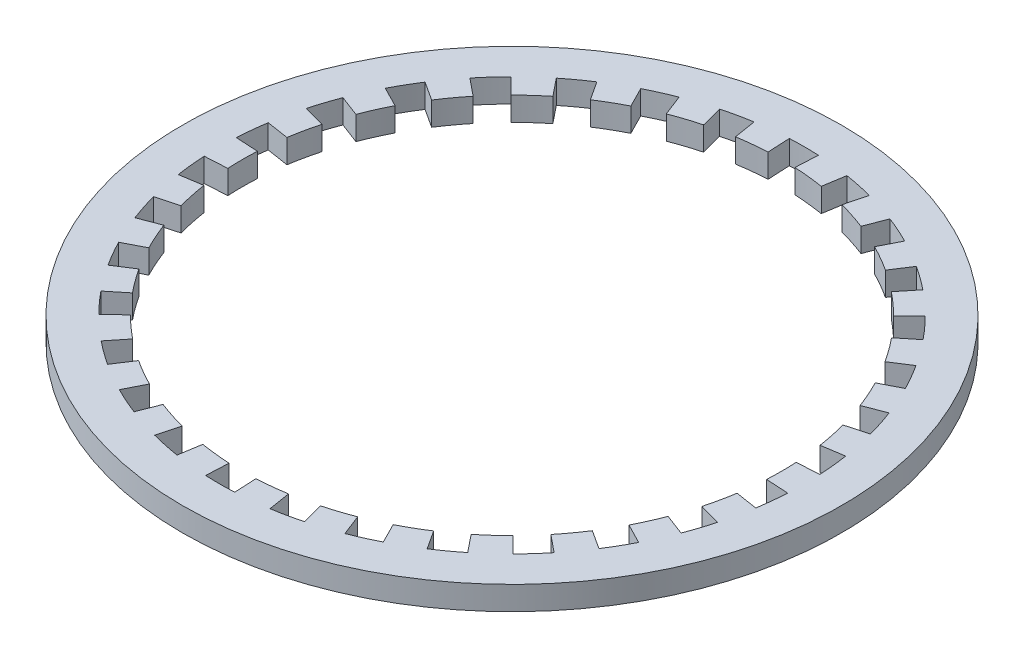
SolidWorks part; units mm, degrees
ref_plane "Front Plane" through (0, 0, 0) normal (0, 0, 1) x (1, 0, 0)
ref_plane "Top Plane" through (0, 0, 0) normal (0, 1, 0) x (1, 0, 0)
ref_plane "Right Plane" through (0, 0, 0) normal (1, 0, 0) x (0, 0, -1)
sketch "Sketch1" plane through (0, 0, 0) normal (0, 1, 0) x (1, 0, 0)
  circle A0 centre (0, 0) radius 7.94
  circle A1 centre (0, 0) radius 6.5
  dimension "D1" = 15.88
  dimension "D2" = 13
extrude "Boss-Extrude1" add sketch "Sketch1" along normal blind 0.57
sketch "Sketch2" plane through (0, 0.57, 0) normal (0, 1, 0) x (1, 0, 0)
  line L0 (0, 7.94) -> (0, -7.94) construction
  line L1 (0.35, 7.0313) -> (0, 0) construction
  line L2 (0, 0) -> (-0.35, 7.0313) construction
  line L3 (-0.35, 7.0313) -> (0.35, 7.0313) construction
  line L4 (0, 7.0313) -> (0, 0) construction
  line L5 (-0.35, 7.0313) -> (-0.3232, 6.492)
  line L6 (0.35, 7.0313) -> (0.3232, 6.492)
  line L7 (1.8042, 6.8049) -> (1.6658, 6.2829)
  line L8 (1.1195, 6.9504) -> (1.0337, 6.4173)
  line L9 (3.1796, 6.281) -> (2.9357, 5.7993)
  line L10 (2.5401, 6.5658) -> (2.3453, 6.0621)
  line L11 (4.416, 5.4827) -> (4.0773, 5.0622)
  line L12 (3.8497, 5.8942) -> (3.5544, 5.4421)
  line L13 (5.4595, 4.4448) -> (5.0407, 4.1038)
  line L14 (4.9911, 4.965) -> (4.6082, 4.5841)
  line L15 (6.2643, 3.2125) -> (5.7838, 2.9661)
  line L16 (5.9143, 3.8188) -> (5.4606, 3.5258)
  line L17 (6.7953, 1.8399) -> (6.2741, 1.6988)
  line L18 (6.579, 2.5057) -> (6.0744, 2.3135)
  line L19 (7.0294, 0.3869) -> (6.4902, 0.3572)
  line L20 (6.9562, 1.0831) -> (6.4226, 1)
  line L21 (6.9562, -1.0831) -> (6.4226, -1)
  line L22 (7.0294, -0.3869) -> (6.4902, -0.3572)
  line L23 (6.579, -2.5057) -> (6.0744, -2.3135)
  line L24 (6.7953, -1.8399) -> (6.2741, -1.6988)
  line L25 (5.9143, -3.8188) -> (5.4606, -3.5258)
  line L26 (6.2643, -3.2125) -> (5.7838, -2.9661)
  line L27 (4.9911, -4.965) -> (4.6082, -4.5841)
  line L28 (5.4595, -4.4448) -> (5.0407, -4.1038)
  line L29 (3.8497, -5.8942) -> (3.5544, -5.4421)
  line L30 (4.416, -5.4827) -> (4.0773, -5.0622)
  line L31 (2.5401, -6.5658) -> (2.3453, -6.0621)
  line L32 (3.1796, -6.281) -> (2.9357, -5.7993)
  line L33 (1.1195, -6.9504) -> (1.0337, -6.4173)
  line L34 (1.8042, -6.8049) -> (1.6658, -6.2829)
  line L35 (-0.35, -7.0313) -> (-0.3232, -6.492)
  line L36 (0.35, -7.0313) -> (0.3232, -6.492)
  line L37 (-1.8042, -6.8049) -> (-1.6658, -6.2829)
  line L38 (-1.1195, -6.9504) -> (-1.0337, -6.4173)
  line L39 (-3.1796, -6.281) -> (-2.9357, -5.7993)
  line L40 (-2.5401, -6.5658) -> (-2.3453, -6.0621)
  line L41 (-4.416, -5.4827) -> (-4.0773, -5.0622)
  line L42 (-3.8497, -5.8942) -> (-3.5544, -5.4421)
  line L43 (-5.4595, -4.4448) -> (-5.0407, -4.1038)
  line L44 (-4.9911, -4.965) -> (-4.6082, -4.5841)
  line L45 (-6.2643, -3.2125) -> (-5.7838, -2.9661)
  line L46 (-5.9143, -3.8188) -> (-5.4606, -3.5258)
  line L47 (-6.7953, -1.8399) -> (-6.2741, -1.6988)
  line L48 (-6.579, -2.5057) -> (-6.0744, -2.3135)
  line L49 (-7.0294, -0.3869) -> (-6.4902, -0.3572)
  line L50 (-6.9562, -1.0831) -> (-6.4226, -1)
  line L51 (-6.9562, 1.0831) -> (-6.4226, 1)
  line L52 (-7.0294, 0.3869) -> (-6.4902, 0.3572)
  line L53 (-6.579, 2.5057) -> (-6.0744, 2.3135)
  line L54 (-6.7953, 1.8399) -> (-6.2741, 1.6988)
  line L55 (-5.9143, 3.8188) -> (-5.4606, 3.5258)
  line L56 (-6.2643, 3.2125) -> (-5.7838, 2.9661)
  line L57 (-4.9911, 4.965) -> (-4.6082, 4.5841)
  line L58 (-5.4595, 4.4448) -> (-5.0407, 4.1038)
  line L59 (-3.8497, 5.8942) -> (-3.5544, 5.4421)
  line L60 (-4.416, 5.4827) -> (-4.0773, 5.0622)
  line L61 (-2.5401, 6.5658) -> (-2.3453, 6.0621)
  line L62 (-3.1796, 6.281) -> (-2.9357, 5.7993)
  line L63 (-1.1195, 6.9504) -> (-1.0337, 6.4173)
  line L64 (-1.8042, 6.8049) -> (-1.6658, 6.2829)
  circle A0 centre (0, 0) radius 7.94 construction
  circle A1 centre (0, 0) radius 6.5 construction
  arc A2 (0.3232, 6.492) -> (-0.3232, 6.492) centre (0, 0) ccw
  arc A3 (1.8042, 6.8049) -> (1.1195, 6.9504) centre (0, 0) ccw
  arc A4 (1.6658, 6.2829) -> (1.0337, 6.4173) centre (0, 0) ccw
  circle A5 centre (0, 0) radius 7.04
  arc A6 (0.35, 7.0313) -> (-0.35, 7.0313) centre (0, 0) ccw
  arc A7 (3.1796, 6.281) -> (2.5401, 6.5658) centre (0, 0) ccw
  arc A8 (2.9357, 5.7993) -> (2.3453, 6.0621) centre (0, 0) ccw
  arc A9 (4.416, 5.4827) -> (3.8497, 5.8942) centre (0, 0) ccw
  arc A10 (4.0773, 5.0622) -> (3.5544, 5.4421) centre (0, 0) ccw
  arc A11 (5.4595, 4.4448) -> (4.9911, 4.965) centre (0, 0) ccw
  arc A12 (5.0407, 4.1038) -> (4.6082, 4.5841) centre (0, 0) ccw
  arc A13 (6.2643, 3.2125) -> (5.9143, 3.8188) centre (0, 0) ccw
  arc A14 (5.7838, 2.9661) -> (5.4606, 3.5258) centre (0, 0) ccw
  arc A15 (6.7953, 1.8399) -> (6.579, 2.5057) centre (0, 0) ccw
  arc A16 (6.2741, 1.6988) -> (6.0744, 2.3135) centre (0, 0) ccw
  arc A17 (7.0294, 0.3869) -> (6.9562, 1.0831) centre (0, 0) ccw
  arc A18 (6.4902, 0.3572) -> (6.4226, 1) centre (0, 0) ccw
  arc A19 (6.9562, -1.0831) -> (7.0294, -0.3869) centre (0, 0) ccw
  arc A20 (6.4226, -1) -> (6.4902, -0.3572) centre (0, 0) ccw
  arc A21 (6.579, -2.5057) -> (6.7953, -1.8399) centre (0, 0) ccw
  arc A22 (6.0744, -2.3135) -> (6.2741, -1.6988) centre (0, 0) ccw
  arc A23 (5.9143, -3.8188) -> (6.2643, -3.2125) centre (0, 0) ccw
  arc A24 (5.4606, -3.5258) -> (5.7838, -2.9661) centre (0, 0) ccw
  arc A25 (4.9911, -4.965) -> (5.4595, -4.4448) centre (0, 0) ccw
  arc A26 (4.6082, -4.5841) -> (5.0407, -4.1038) centre (0, 0) ccw
  arc A27 (3.8497, -5.8942) -> (4.416, -5.4827) centre (0, 0) ccw
  arc A28 (3.5544, -5.4421) -> (4.0773, -5.0622) centre (0, 0) ccw
  arc A29 (2.5401, -6.5658) -> (3.1796, -6.281) centre (0, 0) ccw
  arc A30 (2.3453, -6.0621) -> (2.9357, -5.7993) centre (0, 0) ccw
  arc A31 (1.1195, -6.9504) -> (1.8042, -6.8049) centre (0, 0) ccw
  arc A32 (1.0337, -6.4173) -> (1.6658, -6.2829) centre (0, 0) ccw
  arc A33 (-0.35, -7.0313) -> (0.35, -7.0313) centre (0, 0) ccw
  arc A34 (-0.3232, -6.492) -> (0.3232, -6.492) centre (0, 0) ccw
  arc A35 (-1.8042, -6.8049) -> (-1.1195, -6.9504) centre (0, 0) ccw
  arc A36 (-1.6658, -6.2829) -> (-1.0337, -6.4173) centre (0, 0) ccw
  arc A37 (-3.1796, -6.281) -> (-2.5401, -6.5658) centre (0, 0) ccw
  arc A38 (-2.9357, -5.7993) -> (-2.3453, -6.0621) centre (0, 0) ccw
  arc A39 (-4.416, -5.4827) -> (-3.8497, -5.8942) centre (0, 0) ccw
  arc A40 (-4.0773, -5.0622) -> (-3.5544, -5.4421) centre (0, 0) ccw
  arc A41 (-5.4595, -4.4448) -> (-4.9911, -4.965) centre (0, 0) ccw
  arc A42 (-5.0407, -4.1038) -> (-4.6082, -4.5841) centre (0, 0) ccw
  arc A43 (-6.2643, -3.2125) -> (-5.9143, -3.8188) centre (0, 0) ccw
  arc A44 (-5.7838, -2.9661) -> (-5.4606, -3.5258) centre (0, 0) ccw
  arc A45 (-6.7953, -1.8399) -> (-6.579, -2.5057) centre (0, 0) ccw
  arc A46 (-6.2741, -1.6988) -> (-6.0744, -2.3135) centre (0, 0) ccw
  arc A47 (-7.0294, -0.3869) -> (-6.9562, -1.0831) centre (0, 0) ccw
  arc A48 (-6.4902, -0.3572) -> (-6.4226, -1) centre (0, 0) ccw
  arc A49 (-6.9562, 1.0831) -> (-7.0294, 0.3869) centre (0, 0) ccw
  arc A50 (-6.4226, 1) -> (-6.4902, 0.3572) centre (0, 0) ccw
  arc A51 (-6.579, 2.5057) -> (-6.7953, 1.8399) centre (0, 0) ccw
  arc A52 (-6.0744, 2.3135) -> (-6.2741, 1.6988) centre (0, 0) ccw
  arc A53 (-5.9143, 3.8188) -> (-6.2643, 3.2125) centre (0, 0) ccw
  arc A54 (-5.4606, 3.5258) -> (-5.7838, 2.9661) centre (0, 0) ccw
  arc A55 (-4.9911, 4.965) -> (-5.4595, 4.4448) centre (0, 0) ccw
  arc A56 (-4.6082, 4.5841) -> (-5.0407, 4.1038) centre (0, 0) ccw
  arc A57 (-3.8497, 5.8942) -> (-4.416, 5.4827) centre (0, 0) ccw
  arc A58 (-3.5544, 5.4421) -> (-4.0773, 5.0622) centre (0, 0) ccw
  arc A59 (-2.5401, 6.5658) -> (-3.1796, 6.281) centre (0, 0) ccw
  arc A60 (-2.3453, 6.0621) -> (-2.9357, 5.7993) centre (0, 0) ccw
  arc A61 (-1.1195, 6.9504) -> (-1.8042, 6.8049) centre (0, 0) ccw
  arc A62 (-1.0337, 6.4173) -> (-1.6658, 6.2829) centre (0, 0) ccw
  point P132 (0, 0)
  dimension "D2" = 0.7
  dimension "D1" = 0.9
  dimension "D3" = 30
extrude "Cut-Extrude1" cut sketch "Sketch2" against normal through all
